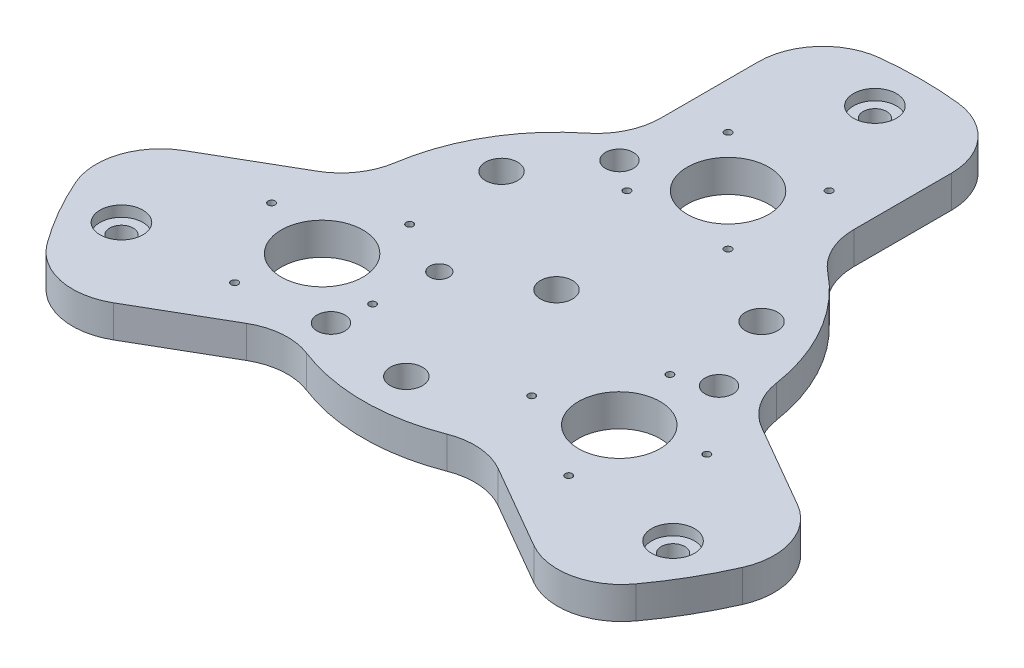
SolidWorks part; units mm, degrees
material "6063-T6"
ref_plane "Front Plane" through (0, 0, 0) normal (0, 0, 1) x (1, 0, 0)
ref_plane "Top Plane" through (0, 0, 0) normal (0, 1, 0) x (1, 0, 0)
ref_plane "Right Plane" through (0, 0, 0) normal (1, 0, 0) x (0, 0, -1)
sketch "Sketch1" plane through (0, 0, 0) normal (0, 1, 0) x (1, 0, 0)
  line L0 (-45, 163.936) -> (-45, 77.9423)
  line L1 (-34.67, -34.67) -> (34.67, -34.67) construction
  line L2 (-34.67, -34.67) -> (-34.67, 34.67) construction
  line L3 (-34.67, 34.67) -> (34.67, 34.67) construction
  line L4 (34.67, -34.67) -> (34.67, 34.67) construction
  line L5 (-34.67, -34.67) -> (34.67, 34.67) construction
  line L6 (-34.67, 34.67) -> (34.67, -34.67) construction
  line L7 (0, 0) -> (0, 170) construction
  line L8 (164.4727, -42.9968) -> (90, 0)
  line L9 (45, 163.936) -> (45, 77.9423)
  line L10 (119.4727, -120.9391) -> (45, -77.9423)
  line L11 (-119.4727, -120.9391) -> (-45, -77.9423)
  line L12 (-164.4727, -42.9968) -> (-90, 0)
  circle A0 centre (0, 0) radius 36.515 construction
  circle A1 centre (0, 0) radius 170 construction
  arc A2 (-45, 77.9423) -> (-82.9156, 35) centre (0, 0) ccw
  circle A3 centre (0, 148.5) radius 10 construction
  arc A4 (45, 163.936) -> (-45, 163.936) centre (0, 0) ccw
  arc A5 (119.4727, -120.9391) -> (164.4727, -42.9968) centre (0, 0) ccw
  arc A6 (-164.4727, -42.9968) -> (-119.4727, -120.9391) centre (0, 0) ccw
  arc A7 (-45, -77.9423) -> (45, -77.9423) centre (0, 0) ccw
  arc A8 (90, 0) -> (45, 77.9423) centre (0, 0) ccw
  arc A10 (-82.9156, -35) -> (-90, 0) centre (0, 0) ccw
  point P26 (0, 0)
  dimension "D1" = 73.03
  dimension "D2" = 340
  dimension "D5" = 20
  dimension "D7" = 180
  dimension "D3" = 69.34
  dimension "D4" = 90
  dimension "D6" = 148.5
  dimension "D8" = 3
extrude "Boss-Extrude1" add sketch "Sketch1" along normal blind 15
fillet "Fillet1" radius 30 12 edges at (-119.4727, 7.5, 120.9391) (-164.4727, 7.5, 42.9968) (-90, 7.5, 0) (-45, 7.5, -77.9423) (-45, 7.5, -163.936) (45, 7.5, -163.936) (45, 7.5, -77.9423) (90, 7.5, 0) (164.4727, 7.5, 42.9968) (119.4727, 7.5, 120.9391) (45, 7.5, 77.9423) (-45, 7.5, 77.9423)
sketch "Sketch4" plane through (0, 15, 0) normal (0, 1, 0) x (1, 0, 0)
  circle A0 centre (0, 148.5) radius 10 construction
  circle A1 centre (0, 148.5) radius 10
extrude "Cut-Extrude1" cut sketch "Sketch4" against normal blind 5
hole_wizard "M10 Clearance Hole1" positions "Sketch5" profile "Sketch6" hole size "M10" standard "ISO" end condition through all
sketch "Sketch5" plane through (0, 15, 0) normal (0, -1, 0) x (-1, 0, 0)
  point P0 (0, 148.5)
sketch "Sketch6" plane through (0, 15, -148.5) normal (1, 0, 0) x (0, 0, 1)
  line L0 (0, 0) -> (0, 15)
  line L1 (0, 15) -> (5.5, 15)
  line L2 (5.5, 15) -> (5.5, 0)
  line L5 (5.5, 0) -> (0, 0)
  line L11 (0, -6.35) -> (0, 107.95) construction
  dimension "Thru Hole Dia." = 11
  dimension "Thru Hole Depth" = 15
ref_axis "Axis1" through (0, 15.75, 0) along (0, -1, 0)
pattern_circular "CirPattern1" count 4 over 360 about axis through (0, 15.75, 0) along (0, -1, 0) skipping 1, 2, 3 of "M10 Clearance Hole1", "Cut-Extrude1"
sketch "Sketch7" plane through (0, 15, 0) normal (0, 1, 0) x (1, 0, 0)
  line L0 (0, 51.8) -> (0, 0) construction
  line L1 (-28.2, 51.8) -> (28.2, 51.8) construction
  line L2 (-28.2, 51.8) -> (-28.2, 108.2) construction
  line L3 (-28.2, 108.2) -> (28.2, 108.2) construction
  line L4 (28.2, 51.8) -> (28.2, 108.2) construction
  line L5 (-28.2, 51.8) -> (28.2, 108.2) construction
  line L6 (-28.2, 108.2) -> (28.2, 51.8) construction
  circle A0 centre (0, 80) radius 19.05
  circle A1 centre (0, 0) radius 125 construction
  dimension "D1" = 38.1
  dimension "D3" = 250
  dimension "D2" = 56.4
  dimension "D4" = 80
extrude "Cut-Extrude2" cut sketch "Sketch7" against normal through all
hole_wizard "M4 Tapped Hole1" positions "Sketch8" profile "Sketch9" tap size "M4" standard "ISO" end condition through all
sketch "Sketch8" plane through (0, 15, 0) normal (0, 1, 0) x (1, 0, 0)
  line L1 (23.57, 56.43) -> (-23.57, 56.43)
  line L2 (23.57, 56.43) -> (23.57, 103.57)
  line L3 (23.57, 103.57) -> (-23.57, 103.57)
  line L4 (-23.57, 56.43) -> (-23.57, 103.57)
  line L5 (23.57, 56.43) -> (-23.57, 103.57) construction
  line L6 (23.57, 103.57) -> (-23.57, 56.43) construction
  line L7 (-23.57, 80) -> (0, 80) construction
  line L8 (0, 80) -> (0, 103.57) construction
  circle A0 centre (0, 80) radius 19.05 construction
  point P2 (-23.57, 103.57)
  point P41 (23.57, 56.43)
  point P42 (23.57, 103.57)
  point P43 (-23.57, 56.43)
  dimension "D1" = 47.14
sketch "Sketch9" plane through (-23.57, 15, -103.57) normal (1, 0, 0) x (0, 0, 1)
  line L0 (0, 0) -> (0, 15)
  line L1 (0, 15) -> (1.65, 15)
  line L2 (1.65, 15) -> (1.65, 0)
  line L5 (1.65, 0) -> (0, 0)
  line L11 (0, -6.35) -> (0, 107.95) construction
  dimension "Thru Tap Drill Dia." = 3.3
  dimension "Thru Tap Drill Depth" = 15
cosmetic thread "Hole Thread1" parameters "D2"=4
cosmetic thread "Hole Thread2" parameters "D2"=4
cosmetic thread "Hole Thread3" parameters "D2"=4
cosmetic thread "Hole Thread4" parameters "D2"=4
pattern_circular "CirPattern2" count 3 over 360 about axis through (0, 0, 0) along (0, 1, 0) of "M4 Tapped Hole1", "Cut-Extrude2"
cosmetic thread "Hole Thread5" parameters "D2"=4
cosmetic thread "Hole Thread6" parameters "D2"=4
cosmetic thread "Hole Thread7" parameters "D2"=4
cosmetic thread "Hole Thread8" parameters "D2"=4
cosmetic thread "Hole Thread9" parameters "D2"=4
cosmetic thread "Hole Thread10" parameters "D2"=4
cosmetic thread "Hole Thread11" parameters "D2"=4
cosmetic thread "Hole Thread12" parameters "D2"=4
pattern_circular "CirPattern3" count 3 over 360 about axis through (0, 0, 0) along (0, 1, 0) of "M10 Clearance Hole1", "Cut-Extrude1"
hole_wizard "M12 Clearance Hole1" positions "Sketch10" profile "Sketch11" hole size "M12" standard "ISO" end condition through all
sketch "Sketch10" plane through (0, 15, 0) normal (0, 1, 0) x (1, 0, 0)
  point P0 (-39.1744, -65.9835)
sketch "Sketch11" plane through (-39.1744, 15, 65.9835) normal (1, 0, 0) x (0, 0, 1)
  line L0 (0, 0) -> (0, 15)
  line L1 (0, 15) -> (6.5, 15)
  line L2 (6.5, 15) -> (6.5, 0)
  line L5 (6.5, 0) -> (0, 0)
  line L11 (0, -6.35) -> (0, 107.95) construction
  dimension "Thru Hole Dia." = 13
  dimension "Thru Hole Depth" = 15
pattern_circular "CirPattern4" count 3 over 360 about axis through (0, 0, 0) along (0, 1, 0) of "M12 Clearance Hole1"
hole_wizard "Ø15.0 (15) Diameter Hole1" positions "Sketch12" profile "Sketch13" hole size "Ø15.0" standard "ISO" end condition through all
sketch "Sketch12" plane through (0, 0, 0) normal (0, -1, 0) x (-1, 0, 0)
  circle A0 centre (0, -70) radius 2.5 construction
  point P0 (0, -70)
sketch "Sketch13" plane through (0, 0, 70) normal (1, 0, 0) x (0, 0, -1)
  line L0 (0, 0) -> (0, 15)
  line L1 (0, 15) -> (7.5, 15)
  line L2 (7.5, 15) -> (7.5, 0)
  line L5 (7.5, 0) -> (0, 0)
  line L11 (0, -6.35) -> (0, 107.95) construction
  dimension "Thru Hole Dia." = 15
  dimension "Thru Hole Depth" = 15
pattern_circular "CirPattern5" count 3 over 360 about axis through (0, 0, 0) along (0, 1, 0) of "Ø15.0 (15) Diameter Hole1"
hole_wizard "Ø15.0 (15) Diameter Hole2" positions "Sketch14" profile "Sketch15" hole size "Ø15.0" standard "ISO" end condition through all
sketch "Sketch14" plane through (0, 0, 0) normal (0, -1, 0) x (-1, 0, 0)
  point P0 (0, 0)
sketch "Sketch15" plane through (0, 0, 0) normal (1, 0, 0) x (0, 0, -1)
  line L0 (0, 0) -> (0, 15)
  line L1 (0, 15) -> (7.5, 15)
  line L2 (7.5, 15) -> (7.5, 0)
  line L5 (7.5, 0) -> (0, 0)
  line L11 (0, -6.35) -> (0, 107.95) construction
  dimension "Thru Hole Dia." = 15
  dimension "Thru Hole Depth" = 15
hole_wizard "Ø9.0 (9) Diameter Hole1" positions "Sketch16" profile "Sketch17" hole size "Ø9.0" standard "ISO" end condition through all
sketch "Sketch16" plane through (0, 0, 0) normal (0, -1, 0) x (-1, 0, 0)
  circle A0 centre (34.641, -20) radius 2.5 construction
  point P0 (34.641, -20)
sketch "Sketch17" plane through (-34.641, 0, 20) normal (1, 0, 0) x (0, 0, -1)
  line L0 (0, 0) -> (0, 15)
  line L1 (0, 15) -> (4.5, 15)
  line L2 (4.5, 15) -> (4.5, 0)
  line L5 (4.5, 0) -> (0, 0)
  line L11 (0, -6.35) -> (0, 107.95) construction
  dimension "Thru Hole Dia." = 9
  dimension "Thru Hole Depth" = 15
